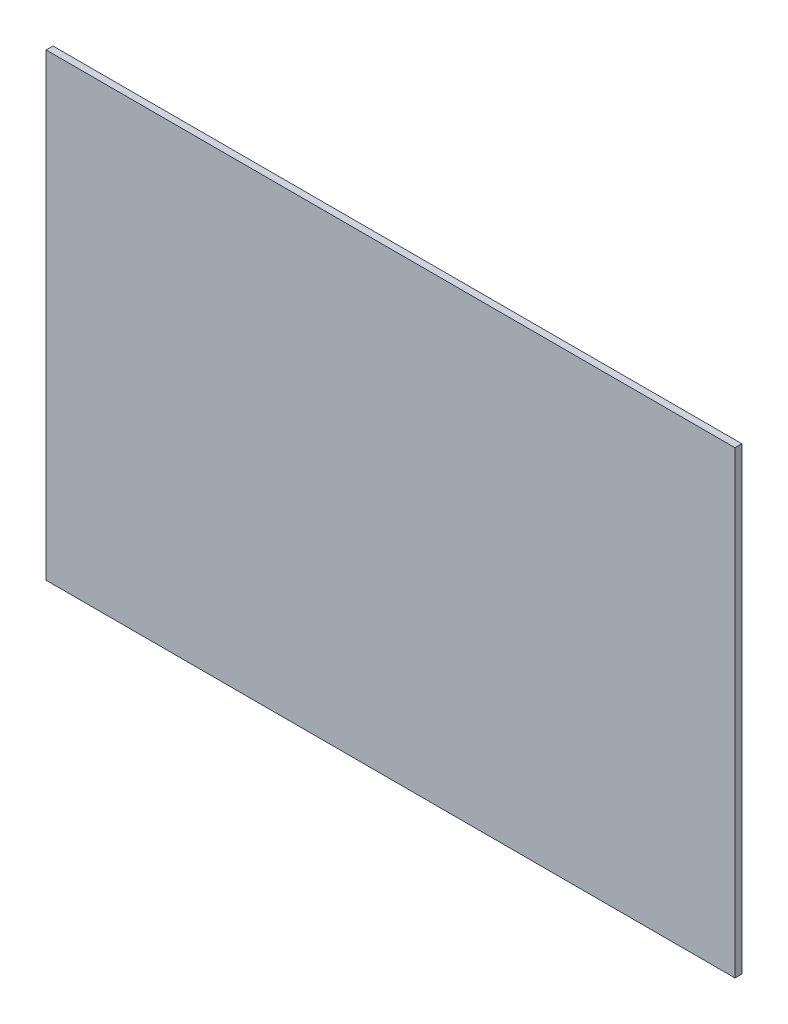
SolidWorks part; units mm, degrees
ref_plane "Plan de face" through (0, 0, 0) normal (0, 0, 1) x (1, 0, 0)
ref_plane "Plan de dessus" through (0, 0, 0) normal (0, 1, 0) x (1, 0, 0)
ref_plane "Plan de droite" through (0, 0, 0) normal (1, 0, 0) x (0, 0, -1)
sketch "Esquisse1" plane through (0, 0, 0) normal (0, 0, 1) x (1, 0, 0)
  line L1 (-59.5483, 184.807) -> (240.4517, 184.807)
  line L2 (-59.5483, 184.807) -> (-59.5483, -15.193)
  line L3 (-59.5483, -15.193) -> (240.4517, -15.193)
  line L4 (240.4517, 184.807) -> (240.4517, -15.193)
extrude "Boss.-Extru.1" add sketch "Esquisse1" along normal blind 3
